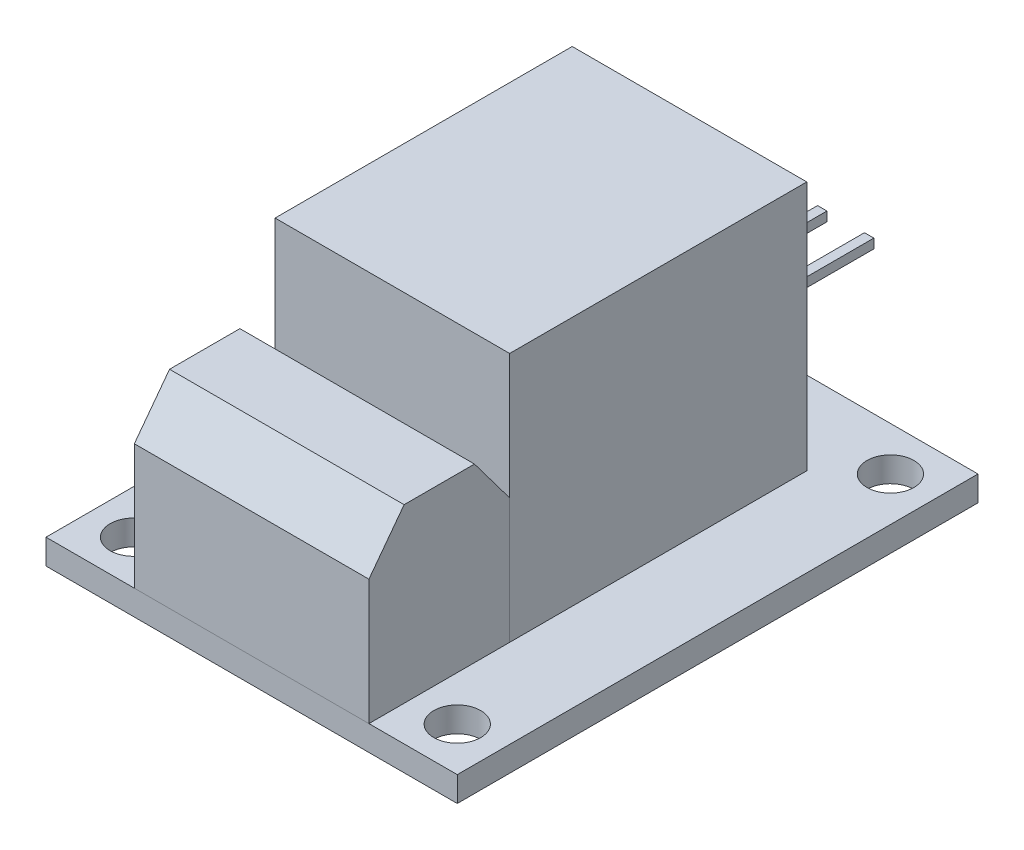
SolidWorks part; units mm, degrees
ref_plane "Front Plane" through (0, 0, 0) normal (0, 0, 1) x (1, 0, 0)
ref_plane "Top Plane" through (0, 0, 0) normal (0, 1, 0) x (1, 0, 0)
ref_plane "Right Plane" through (0, 0, 0) normal (1, 0, 0) x (0, 0, -1)
sketch "Sketch2" plane through (0, 0, 0) normal (0, 1, 0) x (1, 0, 0)
  line L0 (0, 16.65) -> (0, -16.65) construction
  line L1 (16.65, 0) -> (-16.65, 0) construction
  line L3 (-13.15, 16.65) -> (13.15, 16.65)
  line L4 (-13.15, 16.65) -> (-13.15, -16.65)
  line L5 (-13.15, -16.65) -> (13.15, -16.65)
  line L6 (13.15, 16.65) -> (13.15, -16.65)
  dimension "D1" = 33.3
  dimension "D2" = 26.3
extrude "Extrude1" add sketch "Sketch2" along normal blind 1.6
sketch "Sketch3" plane through (0, 1.6, 0) normal (0, 1, 0) x (1, 0, 0)
  line L0 (0, 16.65) -> (0, -25) construction
  line L1 (13.15, 16.65) -> (-13.15, 16.65) construction
  line L2 (13.15, 0) -> (-13.15, 0) construction
  line L3 (13.15, -16.65) -> (13.15, 16.65) construction
  line L4 (-13.15, 16.65) -> (-13.15, -16.65) construction
  line L5 (-13.15, -16.65) -> (13.15, -16.65) construction
  line L6 (-7.5, 11.35) -> (7.5, 11.35)
  line L7 (-7.5, 11.35) -> (-7.5, -7.65)
  line L8 (-7.5, -7.65) -> (7.5, -7.65)
  line L9 (7.5, 11.35) -> (7.5, -7.65)
  dimension "D1" = 19
  dimension "D2" = 15
  dimension "D3" = 9
extrude "Extrude2" add sketch "Sketch3" along normal blind 16
sketch "Sketch4" plane through (0, 1.6, 0) normal (0, 1, 0) x (1, 0, 0)
  line L0 (-13.15, -16.65) -> (13.15, -16.65) construction
  line L1 (-7.5, -7.65) -> (7.5, -7.65)
  line L2 (-7.5, -7.65) -> (-7.5, -16.65)
  line L3 (-7.5, -16.65) -> (7.5, -16.65)
  line L4 (7.5, -7.65) -> (7.5, -16.65)
extrude "Extrude3" add sketch "Sketch4" along normal blind 11 separate body
sketch "Sketch7" plane through (-7.5, 0, 0) normal (-1, 0, 0) x (0, 0, 1)
  line L0 (12.15, 12.6) -> (12.15, 1.6) construction
  line L1 (7.65, 12.6) -> (16.65, 12.6) construction
  line L2 (7.65, 1.6) -> (16.65, 1.6) construction
  line L3 (9.9, 12.6) -> (7.65, 9.6)
  line L4 (7.65, 17.6) -> (7.65, 1.6) construction
  line L5 (7.65, 9.6) -> (7.65, 12.6)
  line L6 (7.65, 12.6) -> (9.9, 12.6)
  line L7 (16.65, 9.6) -> (16.65, 12.6)
  line L8 (16.65, 12.6) -> (14.4, 12.6)
  line L9 (14.4, 12.6) -> (16.65, 9.6)
  dimension "D1" = 2.25
extrude "Extrude5" cut sketch "Sketch7" against normal through all
sketch "Sketch8" plane through (0, 1.6, 0) normal (0, 1, 0) x (1, 0, 0)
  line L0 (13.15, 16.65) -> (-13.15, 16.65) construction
  line L1 (-6.65, 15.35) -> (1.35, 15.35)
  line L2 (-6.65, 15.35) -> (-6.65, 12.35)
  line L3 (-6.65, 12.35) -> (1.35, 12.35)
  line L4 (1.35, 15.35) -> (1.35, 12.35)
  line L5 (-13.15, 16.65) -> (-13.15, -16.65) construction
  dimension "D1" = 8
  dimension "D2" = 3
  dimension "D3" = 1.3
  dimension "D4" = 6.5
extrude "Extrude6" add sketch "Sketch8" along normal blind 4.5
sketch "Sketch9" plane through (0, 0, -15.35) normal (0, 0, -1) x (-1, 0, 0)
  line L0 (2.2088, 5.6353) -> (2.8088, 5.6353)
  line L1 (-0.7912, 5.6353) -> (-0.1912, 5.6353)
  line L2 (-0.7912, 5.6353) -> (-0.7912, 5.0353)
  line L3 (-0.7912, 5.0353) -> (-0.1912, 5.0353)
  line L4 (-0.1912, 5.6353) -> (-0.1912, 5.0353)
  line L5 (2.8088, 5.6353) -> (2.8088, 5.0353)
  line L6 (2.2088, 5.0353) -> (2.8088, 5.0353)
  line L7 (2.2088, 5.6353) -> (2.2088, 5.0353)
  line L8 (5.2088, 5.6353) -> (5.8088, 5.6353)
  line L9 (5.8088, 5.6353) -> (5.8088, 5.0353)
  line L10 (5.2088, 5.0353) -> (5.8088, 5.0353)
  line L11 (5.2088, 5.6353) -> (5.2088, 5.0353)
  dimension "D1" = 0.6
  dimension "D2" = 0.6
  dimension "D3" = 3
extrude "Extrude9" add sketch "Sketch9" along normal blind 7
sketch "Sketch10" plane through (0, 0, 0) normal (0, 1, 0) x (1, 0, 0)
  line L0 (0, -18.078) -> (0, 16.65) construction
  line L1 (13.15, 16.65) -> (-13.15, 16.65) construction
  line L2 (13.15, 0) -> (-13.15, 0) construction
  line L3 (13.15, -16.65) -> (13.15, 16.65) construction
  line L4 (-13.15, 16.65) -> (-13.15, -16.65) construction
  line L5 (-13.15, -16.65) -> (13.15, -16.65) construction
  circle A0 centre (-10.35, -13.85) radius 1.5
  circle A1 centre (10.35, -13.85) radius 1.5
  circle A2 centre (10.35, 13.85) radius 1.5
  circle A3 centre (-10.35, 13.85) radius 1.5
  dimension "D1" = 3
  dimension "D2" = 2.8
  dimension "D3" = 2.8
extrude "Extrude10" cut sketch "Sketch10" along normal through all
